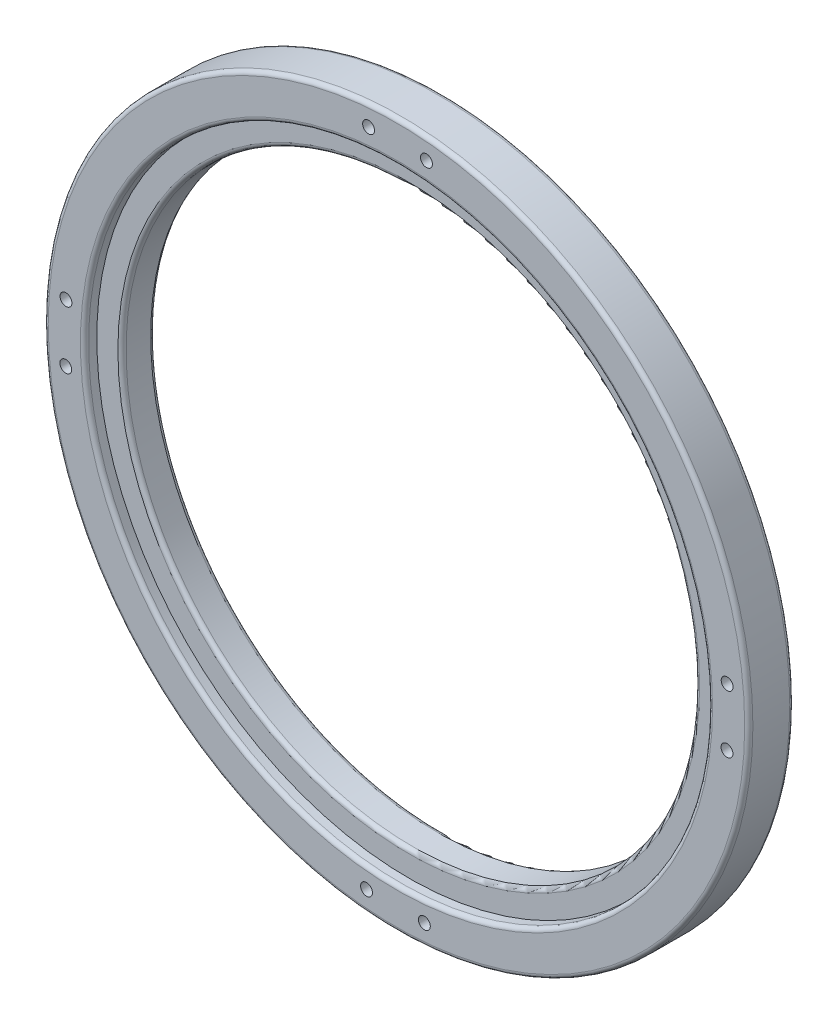
SolidWorks part; units mm, degrees
ref_plane "前视基准面" through (0, 0, 0) normal (0, 0, 1) x (1, 0, 0)
ref_plane "上视基准面" through (0, 0, 0) normal (0, 1, 0) x (1, 0, 0)
ref_plane "右视基准面" through (0, 0, 0) normal (1, 0, 0) x (0, 0, -1)
sketch "草图1" plane through (0, 0, 0) normal (0, 0, 1) x (1, 0, 0)
  circle A0 centre (0, 0) radius 86
  circle A1 centre (0, 0) radius 70
  dimension "D1" = 140
  dimension "D2" = 172
extrude "凸台-拉伸1" add sketch "草图1" along normal blind 8 contours A0 A1
sketch "草图2" plane through (0, 0, 8) normal (0, 0, 1) x (1, 0, 0)
  circle A0 centre (0, 0) radius 76.15
  circle A1 centre (0, 0) radius 86
  dimension "D1" = 152.3
extrude "凸台-拉伸2" add sketch "草图2" along normal blind 3
fillet "圆角1" radius 1 5 edges at (86, 0, 11) (86, 0, 0) (70, 0, 8) (76.15, 0, 11) (70, 0, 0)
hole_wizard "M2.5 间隙孔1" positions "草图3" profile "草图4" hole size "M2.5" standard "ISO" end condition through all
sketch "草图3" plane through (0, 0, 0) normal (0, 0, -1) x (-1, 0, 0)
  line L0 (-7.311, 80.6694) -> (0, 0) construction
  line L2 (6.8081, 80.7134) -> (0, 0) construction
  point P0 (6.8081, 80.7134)
  point P13 (-7.311, 80.6694)
  point P35 (80.7134, -6.8081)
  point P36 (80.6694, 7.311)
  point P37 (-6.8081, -80.7134)
  point P38 (7.311, -80.6694)
  point P39 (-80.7134, 6.8081)
  point P40 (-80.6694, -7.311)
  dimension "D1" = 81
  dimension "D2" = 81
  dimension "D4" = 10
  dimension "D3" = 4
sketch "草图4" plane through (-6.8081, 80.7134, 0) normal (1, 0, 0) x (0, 1, 0)
  line L0 (0, 0) -> (0, 11)
  line L1 (0, 11) -> (1.45, 11)
  line L2 (1.45, 11) -> (1.45, 0.025)
  line L3 (1.45, 0.025) -> (1.475, 0)
  line L5 (1.475, 0) -> (0, 0)
  line L6 (-1.45, 0.025) -> (-1.475, 0) construction
  line L11 (0, -6.35) -> (0, 107.95) construction
  dimension "通孔孔直径" = 2.9
  dimension "通孔孔深度" = 11
  dimension "近端锥形沉头孔直径" = 2.95
  dimension "近端锥形沉头孔角度" = 90
